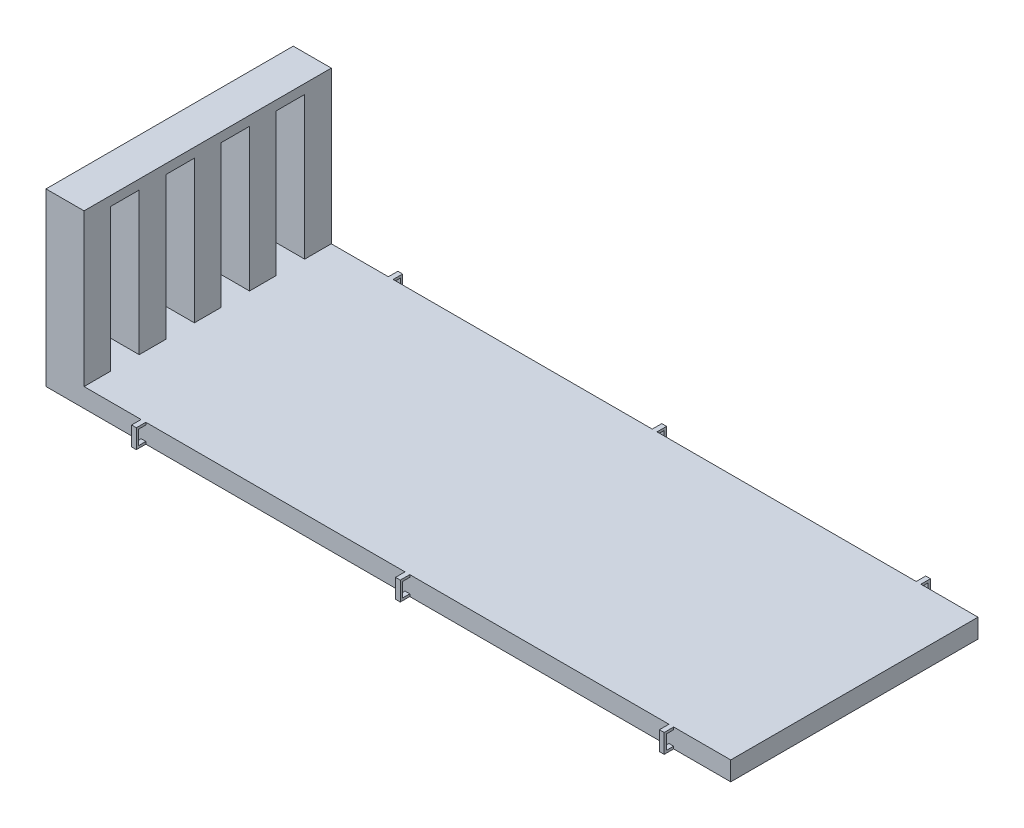
SolidWorks part; units mm, degrees
ref_plane "Front Plane" through (0, 0, 0) normal (0, 0, 1) x (1, 0, 0)
ref_plane "Top Plane" through (0, 0, 0) normal (0, 1, 0) x (1, 0, 0)
ref_plane "Right Plane" through (0, 0, 0) normal (1, 0, 0) x (0, 0, -1)
sketch "Sketch1" plane through (0, 0, 0) normal (0, 1, 0) x (1, 0, 0)
  line L1 (0, 0) -> (914.4, 0)
  line L2 (0, 0) -> (0, -330.2)
  line L3 (0, -330.2) -> (914.4, -330.2)
  line L4 (914.4, 0) -> (914.4, -330.2)
  dimension "D1" = 330.2
  dimension "D2" = 914.4
extrude "Boss-Extrude1" add sketch "Sketch1" along normal blind 25.4
sketch "Sketch2" plane through (0, 25.4, 0) normal (0, 1, 0) x (1, 0, 0)
  line L0 (0, -330.2) -> (914.4, -330.2) construction
  line L1 (0, 0) -> (50.8, 0)
  line L2 (0, 0) -> (0, -330.2)
  line L3 (0, -330.2) -> (50.8, -330.2)
  line L4 (50.8, 0) -> (50.8, -330.2)
  dimension "D1" = 50.8
  dimension "D2" = 330.2
extrude "Boss-Extrude2" add sketch "Sketch2" along normal blind 203.2 contours L3 L4 L1 L2
sketch "Sketch5" plane through (0, 0, 330.2) normal (0, 0, 1) x (1, 0, 0)
  line L0 (50.8, 25.4) -> (914.4, 25.4) construction
  line L1 (127, 25.4) -> (133.35, 25.4)
  line L2 (127, 25.4) -> (127, 0)
  line L3 (127, 0) -> (133.35, 0)
  line L4 (133.35, 25.4) -> (133.35, 0)
  line L5 (0, 0) -> (914.4, 0) construction
  line L6 (133.35, 0) -> (831.85, 0) construction
  line L7 (479.425, 25.4) -> (485.775, 25.4)
  line L8 (479.425, 25.4) -> (479.425, 0)
  line L9 (479.425, 0) -> (485.775, 0)
  line L10 (485.775, 25.4) -> (485.775, 0)
  line L11 (831.85, 25.4) -> (838.2, 25.4)
  line L12 (831.85, 25.4) -> (831.85, 0)
  line L13 (831.85, 0) -> (838.2, 0)
  line L14 (838.2, 25.4) -> (838.2, 0)
  line L15 (914.4, 25.4) -> (914.4, 0) construction
  line L16 (50.8, 228.6) -> (50.8, 25.4) construction
  line L17 (479.425, 18.755) -> (485.775, 18.755) construction
  point P22 (482.6, 18.755)
  point P23 (482.6, 0)
  dimension "D1" = 6.35
  dimension "D2" = 6.35
  dimension "D3" = 6.35
  dimension "D4" = 76.2
  dimension "D5" = 76.2
extrude "Boss-Extrude3" add sketch "Sketch5" along normal blind 12.7
sketch "Sketch6" plane through (133.35, 0, 0) normal (1, 0, 0) x (0, 0, -1)
  line L0 (-330.2, 0) -> (-330.2, 25.4) construction
  line L1 (-330.2, 22.225) -> (-339.725, 22.225)
  line L2 (-330.2, 22.225) -> (-330.2, 3.175)
  line L3 (-330.2, 3.175) -> (-339.725, 3.175)
  line L4 (-339.725, 22.225) -> (-339.725, 3.175)
  line L5 (-342.9, 25.4) -> (-330.2, 25.4) construction
  line L6 (-342.9, 0) -> (-342.9, 25.4) construction
  line L7 (-342.9, 0) -> (-330.2, 0) construction
  dimension "D1" = 3.175
  dimension "D2" = 3.175
  dimension "D3" = 3.175
extrude "Cut-Extrude1" cut sketch "Sketch6" against normal blind 6.35
sketch "Sketch7" plane through (485.775, 0, 0) normal (1, 0, 0) x (0, 0, -1)
  line L0 (-330.2, 0) -> (-330.2, 25.4) construction
  line L1 (-330.2, 22.225) -> (-339.725, 22.225)
  line L2 (-330.2, 22.225) -> (-330.2, 3.175)
  line L3 (-330.2, 3.175) -> (-339.725, 3.175)
  line L4 (-339.725, 22.225) -> (-339.725, 3.175)
  line L5 (-342.9, 25.4) -> (-330.2, 25.4) construction
  line L6 (-342.9, 0) -> (-330.2, 0) construction
  line L7 (-342.9, 0) -> (-342.9, 25.4) construction
  point P8 (-336.55, 25.4)
  dimension "D1" = 3.175
  dimension "D2" = 3.175
  dimension "D3" = 3.175
extrude "Cut-Extrude2" cut sketch "Sketch7" against normal blind 6.35
sketch "Sketch8" plane through (838.2, 0, 0) normal (1, 0, 0) x (0, 0, -1)
  line L0 (-330.2, 0) -> (-330.2, 25.4) construction
  line L1 (-330.2, 22.225) -> (-339.7174, 22.225)
  line L2 (-330.2, 22.225) -> (-330.2, 3.175)
  line L3 (-330.2, 3.175) -> (-339.7174, 3.175)
  line L4 (-339.7174, 22.225) -> (-339.7174, 3.175)
  line L5 (-342.9, 25.4) -> (-330.2, 25.4) construction
  line L6 (-342.9, 0) -> (-330.2, 0) construction
  line L7 (-342.9, 0) -> (-342.9, 25.4) construction
  dimension "D1" = 3.175
  dimension "D2" = 3.175
  dimension "D3" = 3.1826
extrude "Cut-Extrude3" cut sketch "Sketch8" against normal blind 6.35
sketch "Sketch9" plane through (0, 0, 0) normal (0, 0, -1) x (-1, 0, 0)
  line L0 (-914.4, 25.4) -> (-50.8, 25.4) construction
  line L1 (-838.2, 25.4) -> (-831.85, 25.4)
  line L2 (-838.2, 25.4) -> (-838.2, 0)
  line L3 (-838.2, 0) -> (-831.85, 0)
  line L4 (-831.85, 25.4) -> (-831.85, 0)
  line L5 (-914.4, 0) -> (0, 0) construction
  line L6 (-50.8, 228.6) -> (-50.8, 25.4) construction
  line L7 (-485.775, 25.4) -> (-479.425, 25.4)
  line L8 (-485.775, 25.4) -> (-485.775, 0)
  line L9 (-485.775, 0) -> (-479.425, 0)
  line L10 (-479.425, 25.4) -> (-479.425, 0)
  line L11 (-133.35, 25.4) -> (-127, 25.4)
  line L12 (-133.35, 25.4) -> (-133.35, 0)
  line L13 (-133.35, 0) -> (-127, 0)
  line L14 (-127, 25.4) -> (-127, 0)
  line L15 (-914.4, 25.4) -> (-914.4, 0) construction
  line L16 (-831.85, 0) -> (-133.35, 0) construction
  line L17 (-485.775, 17.0607) -> (-479.425, 17.0607) construction
  point P22 (-482.6, 17.0607)
  point P23 (-482.6, 0)
  dimension "D1" = 76.2
  dimension "D2" = 6.35
  dimension "D3" = 6.35
  dimension "D4" = 6.35
  dimension "D5" = 76.2
extrude "Boss-Extrude4" add sketch "Sketch9" along normal blind 12.7
sketch "Sketch10" plane through (133.35, 0, 0) normal (1, 0, 0) x (0, 0, -1)
  line L0 (0, 25.4) -> (0, 0) construction
  line L1 (0, 22.225) -> (9.525, 22.225)
  line L2 (0, 22.225) -> (0, 3.175)
  line L3 (0, 3.175) -> (9.525, 3.175)
  line L4 (9.525, 22.225) -> (9.525, 3.175)
  line L5 (12.7, 25.4) -> (0, 25.4) construction
  line L6 (12.7, 25.4) -> (12.7, 0) construction
  line L7 (12.7, 0) -> (0, 0) construction
  dimension "D1" = 3.175
  dimension "D2" = 3.175
  dimension "D3" = 3.175
extrude "Cut-Extrude4" cut sketch "Sketch10" against normal blind 6.35
sketch "Sketch11" plane through (485.775, 0, 0) normal (1, 0, 0) x (0, 0, -1)
  line L0 (0, 25.4) -> (0, 0) construction
  line L1 (0, 22.225) -> (9.525, 22.225)
  line L2 (0, 22.225) -> (0, 3.175)
  line L3 (0, 3.175) -> (9.525, 3.175)
  line L4 (9.525, 22.225) -> (9.525, 3.175)
  line L5 (12.7, 25.4) -> (0, 25.4) construction
  line L6 (12.7, 25.4) -> (12.7, 0) construction
  line L7 (12.7, 0) -> (0, 0) construction
  dimension "D1" = 3.175
  dimension "D2" = 3.175
  dimension "D3" = 3.175
extrude "Cut-Extrude5" cut sketch "Sketch11" against normal blind 6.35
sketch "Sketch12" plane through (838.2, 0, 0) normal (1, 0, 0) x (0, 0, -1)
  line L0 (0, 25.4) -> (0, 0) construction
  line L1 (0, 22.225) -> (9.525, 22.225)
  line L2 (0, 22.225) -> (0, 3.175)
  line L3 (0, 3.175) -> (9.525, 3.175)
  line L4 (9.525, 22.225) -> (9.525, 3.175)
  line L5 (12.7, 25.4) -> (0, 25.4) construction
  line L6 (12.7, 25.4) -> (12.7, 0) construction
  line L7 (12.7, 0) -> (0, 0) construction
  dimension "D1" = 3.175
  dimension "D2" = 3.175
  dimension "D3" = 3.175
extrude "Cut-Extrude6" cut sketch "Sketch12" against normal blind 6.35
sketch "Sketch15" plane through (50.8, 0, 0) normal (1, 0, 0) x (0, 0, -1)
  line L0 (-330.2, 25.4) -> (0, 25.4) construction
  line L1 (-294.64, 25.4) -> (-256.54, 25.4)
  line L2 (-294.64, 25.4) -> (-294.64, 215.9)
  line L3 (-294.64, 215.9) -> (-256.54, 215.9)
  line L4 (-256.54, 25.4) -> (-256.54, 215.9)
  line L5 (-182.88, 133.482) -> (-147.32, 133.482) construction
  line L6 (-220.98, 25.4) -> (-220.98, 215.9)
  line L7 (-220.98, 25.4) -> (-182.88, 25.4)
  line L8 (-182.88, 25.4) -> (-182.88, 215.9)
  line L9 (-220.98, 215.9) -> (-182.88, 215.9)
  line L10 (-147.32, 25.4) -> (-147.32, 215.9)
  line L11 (-147.32, 25.4) -> (-109.22, 25.4)
  line L12 (-109.22, 25.4) -> (-109.22, 215.9)
  line L13 (-147.32, 215.9) -> (-109.22, 215.9)
  line L14 (-73.66, 25.4) -> (-73.66, 215.9)
  line L15 (-73.66, 25.4) -> (-35.56, 25.4)
  line L16 (-35.56, 25.4) -> (-35.56, 215.9)
  line L17 (-73.66, 215.9) -> (-35.56, 215.9)
  line L18 (-109.22, 131.4796) -> (-73.66, 131.4796) construction
  line L19 (-330.2, 136.6505) -> (-294.64, 136.6505) construction
  line L20 (-330.2, 228.6) -> (-330.2, 25.4) construction
  line L21 (-256.54, 136.6505) -> (-220.98, 136.6505) construction
  line L22 (-35.56, 131.4796) -> (0, 131.4796) construction
  line L23 (0, 228.6) -> (0, 25.4) construction
  dimension "D1" = 38.1
  dimension "D2" = 190.5
  dimension "D4" = 4
extrude "Cut-Extrude7" cut sketch "Sketch15" against normal through all
sketch "Sketch16" plane through (0, 0, 0) normal (0, -1, 0) x (1, 0, 0)
  line L1 (609.6, 215.9) -> (762, 215.9)
  line L2 (609.6, 215.9) -> (609.6, 114.3)
  line L3 (609.6, 114.3) -> (762, 114.3)
  line L4 (762, 215.9) -> (762, 114.3)
  line L5 (914.4, 330.2) -> (914.4, 0) construction
  line L6 (522.142, 330.2) -> (522.142, 0) construction
  line L7 (485.775, 330.2) -> (831.85, 330.2) construction
  line L8 (831.85, 0) -> (485.775, 0) construction
  point P4 (609.6, 165.1)
  point P5 (522.142, 165.1)
  dimension "D1" = 152.4
  dimension "D2" = 101.6
  dimension "D3" = 152.4
extrude "Boss-Extrude5" add sketch "Sketch16" along normal blind 76.2
